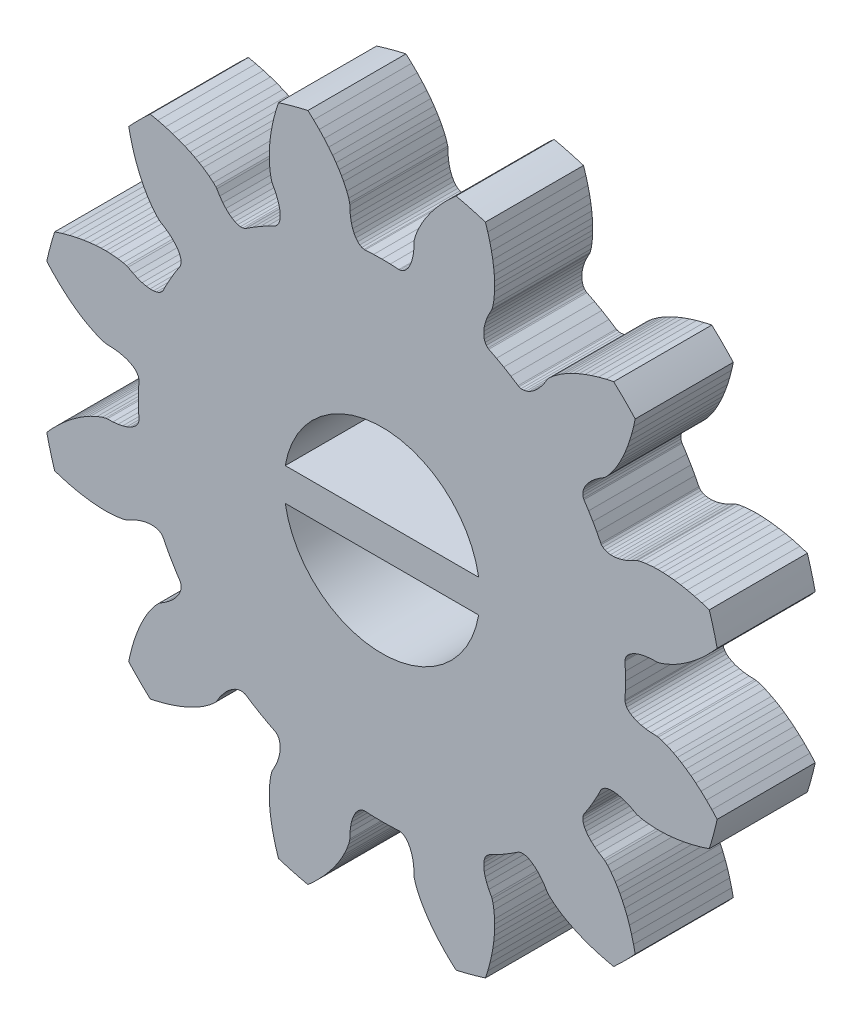
SolidWorks part; units mm, degrees
ref_plane "Płaszczyzna przednia" through (0, 0, 0) normal (0, 0, 1) x (1, 0, 0)
ref_plane "Płaszczyzna górna" through (0, 0, 0) normal (0, 1, 0) x (1, 0, 0)
ref_plane "Płaszczyzna prawa" through (0, 0, 0) normal (1, 0, 0) x (0, 0, -1)
sketch "szkic" plane through (0, 0, 0) normal (0, 0, 1) x (1, 0, 0)
  line L0 (13.3041, -6.8561) -> (13.3646, -6.6243)
  line L1 (13.3646, -6.6243) -> (13.4305, -6.4094)
  line L2 (13.4305, -6.4094) -> (13.5003, -6.2115)
  line L3 (13.5003, -6.2115) -> (13.5727, -6.0307)
  line L4 (13.5727, -6.0307) -> (13.6464, -5.8671)
  line L5 (13.6464, -5.8671) -> (13.7211, -5.718)
  line L6 (13.7211, -5.718) -> (13.7935, -5.5877)
  line L7 (13.7935, -5.5877) -> (13.8642, -5.472)
  line L8 (13.8642, -5.472) -> (13.9934, -5.2871)
  line L9 (13.9934, -5.2871) -> (14.1006, -5.158)
  line L10 (14.1006, -5.158) -> (14.1765, -5.0806)
  line L11 (14.1765, -5.0806) -> (14.2153, -5.0522)
  line L12 (14.2153, -5.0522) -> (14.3621, -4.9616)
  line L13 (14.3621, -4.9616) -> (14.4896, -4.8682)
  line L14 (14.4896, -4.8682) -> (14.5978, -4.7734)
  line L15 (14.5978, -4.7734) -> (14.6868, -4.6788)
  line L16 (14.6868, -4.6788) -> (14.7569, -4.5857)
  line L17 (14.7569, -4.5857) -> (14.8083, -4.4956)
  line L18 (14.8083, -4.4956) -> (14.8415, -4.4098)
  line L19 (14.8415, -4.4098) -> (14.8569, -4.3297)
  line L20 (14.8569, -4.3297) -> (14.8551, -4.2567)
  line L21 (14.8551, -4.2567) -> (14.8367, -4.192)
  line L22 (14.8367, -4.192) -> (14.8215, -4.1631)
  line L23 (14.8215, -4.1631) -> (14.6788, -3.9428)
  line L24 (14.6788, -3.9428) -> (14.5481, -3.725)
  line L25 (14.5481, -3.725) -> (14.4249, -3.5029)
  line L26 (14.4249, -3.5029) -> (14.3054, -3.2691)
  line L27 (14.3054, -3.2691) -> (14.288, -3.2416)
  line L28 (14.288, -3.2416) -> (14.2411, -3.1933)
  line L29 (14.2411, -3.1933) -> (14.1788, -3.1552)
  line L30 (14.1788, -3.1552) -> (14.1017, -3.1285)
  line L31 (14.1017, -3.1285) -> (14.0109, -3.1144)
  line L32 (14.0109, -3.1144) -> (13.9071, -3.1138)
  line L33 (13.9071, -3.1138) -> (13.7915, -3.128)
  line L34 (13.7915, -3.128) -> (13.665, -3.1577)
  line L35 (13.665, -3.1577) -> (13.5289, -3.2041)
  line L36 (13.5289, -3.2041) -> (13.3842, -3.2678)
  line L37 (13.3842, -3.2678) -> (13.2323, -3.3497)
  line L38 (13.2323, -3.3497) -> (13.1884, -3.369)
  line L39 (13.1884, -3.369) -> (13.0833, -3.3961)
  line L40 (13.0833, -3.3961) -> (12.918, -3.4244)
  line L41 (12.918, -3.4244) -> (12.6932, -3.4438)
  line L42 (12.6932, -3.4438) -> (12.5577, -3.4472)
  line L43 (12.5577, -3.4472) -> (12.4086, -3.4447)
  line L44 (12.4086, -3.4447) -> (12.2421, -3.4349)
  line L45 (12.2421, -3.4349) -> (12.0636, -3.4169)
  line L46 (12.0636, -3.4169) -> (11.8708, -3.3892)
  line L47 (11.8708, -3.3892) -> (11.6645, -3.3507)
  line L48 (11.6645, -3.3507) -> (11.4455, -3.3003)
  line L49 (11.4455, -3.3003) -> (11.2145, -3.2368)
  line L50 (11.2145, -3.2368) -> (10.9882, -3.1643)
  line L51 (10.7474, -2.2655) -> (10.9071, -2.0896)
  line L52 (10.9071, -2.0896) -> (11.0754, -1.9191)
  line L53 (11.0754, -1.9191) -> (11.2399, -1.7659)
  line L54 (11.2399, -1.7659) -> (11.3993, -1.6295)
  line L55 (11.3993, -1.6295) -> (11.5524, -1.5091)
  line L56 (11.5524, -1.5091) -> (11.698, -1.4042)
  line L57 (11.698, -1.4042) -> (11.8373, -1.3125)
  line L58 (11.8373, -1.3125) -> (11.9651, -1.2358)
  line L59 (11.9651, -1.2358) -> (12.0842, -1.171)
  line L60 (12.0842, -1.171) -> (12.2886, -1.0754)
  line L61 (12.2886, -1.0754) -> (12.4459, -1.0172)
  line L62 (12.4459, -1.0172) -> (12.5504, -0.9882)
  line L63 (12.5504, -0.9882) -> (12.5981, -0.983)
  line L64 (12.5981, -0.983) -> (12.7706, -0.9779)
  line L65 (12.7706, -0.9779) -> (12.9278, -0.9608)
  line L66 (12.9278, -0.9608) -> (13.0688, -0.9328)
  line L67 (13.0688, -0.9328) -> (13.1933, -0.8953)
  line L68 (13.1933, -0.8953) -> (13.3005, -0.8498)
  line L69 (13.3005, -0.8498) -> (13.3901, -0.7974)
  line L70 (13.3901, -0.7974) -> (13.4617, -0.7397)
  line L71 (13.4617, -0.7397) -> (13.515, -0.6781)
  line L72 (13.515, -0.6781) -> (13.55, -0.6139)
  line L73 (13.55, -0.6139) -> (13.5665, -0.5487)
  line L74 (13.5665, -0.5487) -> (13.5677, -0.5161)
  line L75 (13.5677, -0.5161) -> (13.5543, -0.2539)
  line L76 (13.5543, -0.2539) -> (13.55, 0)
  line L77 (13.55, 0) -> (13.5543, 0.2539)
  line L78 (13.5543, 0.2539) -> (13.5677, 0.5161)
  line L79 (13.5677, 0.5161) -> (13.5665, 0.5487)
  line L80 (13.5665, 0.5487) -> (13.55, 0.6139)
  line L81 (13.55, 0.6139) -> (13.515, 0.6781)
  line L82 (13.515, 0.6781) -> (13.4617, 0.7397)
  line L83 (13.4617, 0.7397) -> (13.3901, 0.7974)
  line L84 (13.3901, 0.7974) -> (13.3005, 0.8498)
  line L85 (13.3005, 0.8498) -> (13.1933, 0.8953)
  line L86 (13.1933, 0.8953) -> (13.0688, 0.9328)
  line L87 (13.0688, 0.9328) -> (12.9278, 0.9608)
  line L88 (12.9278, 0.9608) -> (12.7706, 0.9779)
  line L89 (12.7706, 0.9779) -> (12.5981, 0.983)
  line L90 (12.5981, 0.983) -> (12.5504, 0.9882)
  line L91 (12.5504, 0.9882) -> (12.4459, 1.0172)
  line L92 (12.4459, 1.0172) -> (12.2886, 1.0754)
  line L93 (12.2886, 1.0754) -> (12.0842, 1.171)
  line L94 (12.0842, 1.171) -> (11.9651, 1.2358)
  line L95 (11.9651, 1.2358) -> (11.8373, 1.3125)
  line L96 (11.8373, 1.3125) -> (11.698, 1.4042)
  line L97 (11.698, 1.4042) -> (11.5524, 1.5091)
  line L98 (11.5524, 1.5091) -> (11.3993, 1.6295)
  line L99 (11.3993, 1.6295) -> (11.2399, 1.7659)
  line L100 (11.2399, 1.7659) -> (11.0754, 1.9191)
  line L101 (11.0754, 1.9191) -> (10.9071, 2.0896)
  line L102 (10.9071, 2.0896) -> (10.7474, 2.2655)
  line L103 (10.9882, 3.1643) -> (11.2145, 3.2368)
  line L104 (11.2145, 3.2368) -> (11.4455, 3.3003)
  line L105 (11.4455, 3.3003) -> (11.6645, 3.3507)
  line L106 (11.6645, 3.3507) -> (11.8708, 3.3892)
  line L107 (11.8708, 3.3892) -> (12.0636, 3.4169)
  line L108 (12.0636, 3.4169) -> (12.2421, 3.4349)
  line L109 (12.2421, 3.4349) -> (12.4086, 3.4447)
  line L110 (12.4086, 3.4447) -> (12.5577, 3.4472)
  line L111 (12.5577, 3.4472) -> (12.6932, 3.4438)
  line L112 (12.6932, 3.4438) -> (12.918, 3.4244)
  line L113 (12.918, 3.4244) -> (13.0833, 3.3961)
  line L114 (13.0833, 3.3961) -> (13.1884, 3.369)
  line L115 (13.1884, 3.369) -> (13.2323, 3.3497)
  line L116 (13.2323, 3.3497) -> (13.3842, 3.2678)
  line L117 (13.3842, 3.2678) -> (13.5289, 3.2041)
  line L118 (13.5289, 3.2041) -> (13.665, 3.1577)
  line L119 (13.665, 3.1577) -> (13.7915, 3.128)
  line L120 (13.7915, 3.128) -> (13.9071, 3.1138)
  line L121 (13.9071, 3.1138) -> (14.0109, 3.1144)
  line L122 (14.0109, 3.1144) -> (14.1017, 3.1285)
  line L123 (14.1017, 3.1285) -> (14.1788, 3.1552)
  line L124 (14.1788, 3.1552) -> (14.2411, 3.1933)
  line L125 (14.2411, 3.1933) -> (14.288, 3.2416)
  line L126 (14.288, 3.2416) -> (14.3054, 3.2691)
  line L127 (14.3054, 3.2691) -> (14.4249, 3.5029)
  line L128 (14.4249, 3.5029) -> (14.5481, 3.725)
  line L129 (14.5481, 3.725) -> (14.6788, 3.9428)
  line L130 (14.6788, 3.9428) -> (14.8215, 4.1631)
  line L131 (14.8215, 4.1631) -> (14.8367, 4.192)
  line L132 (14.8367, 4.192) -> (14.8551, 4.2567)
  line L133 (14.8551, 4.2567) -> (14.8569, 4.3297)
  line L134 (14.8569, 4.3297) -> (14.8415, 4.4098)
  line L135 (14.8415, 4.4098) -> (14.8083, 4.4956)
  line L136 (14.8083, 4.4956) -> (14.7569, 4.5857)
  line L137 (14.7569, 4.5857) -> (14.6868, 4.6788)
  line L138 (14.6868, 4.6788) -> (14.5978, 4.7734)
  line L139 (14.5978, 4.7734) -> (14.4896, 4.8682)
  line L140 (14.4896, 4.8682) -> (14.3621, 4.9616)
  line L141 (14.3621, 4.9616) -> (14.2153, 5.0522)
  line L142 (14.2153, 5.0522) -> (14.1765, 5.0806)
  line L143 (14.1765, 5.0806) -> (14.1006, 5.158)
  line L144 (14.1006, 5.158) -> (13.9934, 5.2871)
  line L145 (13.9934, 5.2871) -> (13.8642, 5.472)
  line L146 (13.8642, 5.472) -> (13.7935, 5.5877)
  line L147 (13.7935, 5.5877) -> (13.7211, 5.718)
  line L148 (13.7211, 5.718) -> (13.6464, 5.8671)
  line L149 (13.6464, 5.8671) -> (13.5727, 6.0307)
  line L150 (13.5727, 6.0307) -> (13.5003, 6.2115)
  line L151 (13.5003, 6.2115) -> (13.4305, 6.4094)
  line L152 (13.4305, 6.4094) -> (13.3646, 6.6243)
  line L153 (13.3646, 6.6243) -> (13.3041, 6.8561)
  line L154 (13.3041, 6.8561) -> (13.2537, 7.0883)
  line L155 (13.9117, 7.7463) -> (14.1439, 7.6959)
  line L156 (14.1439, 7.6959) -> (14.3757, 7.6354)
  line L157 (14.3757, 7.6354) -> (14.5906, 7.5695)
  line L158 (14.5906, 7.5695) -> (14.7885, 7.4997)
  line L159 (14.7885, 7.4997) -> (14.9693, 7.4273)
  line L160 (14.9693, 7.4273) -> (15.1329, 7.3536)
  line L161 (15.1329, 7.3536) -> (15.282, 7.2789)
  line L162 (15.282, 7.2789) -> (15.4123, 7.2065)
  line L163 (15.4123, 7.2065) -> (15.528, 7.1358)
  line L164 (15.528, 7.1358) -> (15.7129, 7.0066)
  line L165 (15.7129, 7.0066) -> (15.842, 6.8994)
  line L166 (15.842, 6.8994) -> (15.9194, 6.8235)
  line L167 (15.9194, 6.8235) -> (15.9478, 6.7847)
  line L168 (15.9478, 6.7847) -> (16.0384, 6.6379)
  line L169 (16.0384, 6.6379) -> (16.1318, 6.5104)
  line L170 (16.1318, 6.5104) -> (16.2266, 6.4022)
  line L171 (16.2266, 6.4022) -> (16.3212, 6.3132)
  line L172 (16.3212, 6.3132) -> (16.4143, 6.2431)
  line L173 (16.4143, 6.2431) -> (16.5044, 6.1917)
  line L174 (16.5044, 6.1917) -> (16.5902, 6.1585)
  line L175 (16.5902, 6.1585) -> (16.6703, 6.1431)
  line L176 (16.6703, 6.1431) -> (16.7433, 6.1449)
  line L177 (16.7433, 6.1449) -> (16.808, 6.1633)
  line L178 (16.808, 6.1633) -> (16.8369, 6.1785)
  line L179 (16.8369, 6.1785) -> (17.0572, 6.3212)
  line L180 (17.0572, 6.3212) -> (17.275, 6.4519)
  line L181 (17.275, 6.4519) -> (17.4971, 6.5751)
  line L182 (17.4971, 6.5751) -> (17.7309, 6.6946)
  line L183 (17.7309, 6.6946) -> (17.7584, 6.712)
  line L184 (17.7584, 6.712) -> (17.8067, 6.7589)
  line L185 (17.8067, 6.7589) -> (17.8448, 6.8212)
  line L186 (17.8448, 6.8212) -> (17.8715, 6.8983)
  line L187 (17.8715, 6.8983) -> (17.8856, 6.9891)
  line L188 (17.8856, 6.9891) -> (17.8862, 7.0929)
  line L189 (17.8862, 7.0929) -> (17.872, 7.2085)
  line L190 (17.872, 7.2085) -> (17.8423, 7.335)
  line L191 (17.8423, 7.335) -> (17.7959, 7.4711)
  line L192 (17.7959, 7.4711) -> (17.7322, 7.6158)
  line L193 (17.7322, 7.6158) -> (17.6503, 7.7677)
  line L194 (17.6503, 7.7677) -> (17.631, 7.8116)
  line L195 (17.631, 7.8116) -> (17.6039, 7.9167)
  line L196 (17.6039, 7.9167) -> (17.5756, 8.082)
  line L197 (17.5756, 8.082) -> (17.5562, 8.3068)
  line L198 (17.5562, 8.3068) -> (17.5528, 8.4423)
  line L199 (17.5528, 8.4423) -> (17.5553, 8.5914)
  line L200 (17.5553, 8.5914) -> (17.5651, 8.7579)
  line L201 (17.5651, 8.7579) -> (17.5831, 8.9364)
  line L202 (17.5831, 8.9364) -> (17.6108, 9.1292)
  line L203 (17.6108, 9.1292) -> (17.6493, 9.3355)
  line L204 (17.6493, 9.3355) -> (17.6997, 9.5545)
  line L205 (17.6997, 9.5545) -> (17.7632, 9.7855)
  line L206 (17.7632, 9.7855) -> (17.8357, 10.0118)
  line L207 (18.7345, 10.2526) -> (18.9104, 10.0929)
  line L208 (18.9104, 10.0929) -> (19.0809, 9.9246)
  line L209 (19.0809, 9.9246) -> (19.2341, 9.7601)
  line L210 (19.2341, 9.7601) -> (19.3706, 9.6007)
  line L211 (19.3706, 9.6007) -> (19.4909, 9.4476)
  line L212 (19.4909, 9.4476) -> (19.5958, 9.302)
  line L213 (19.5958, 9.302) -> (19.6875, 9.1627)
  line L214 (19.6875, 9.1627) -> (19.7642, 9.0349)
  line L215 (19.7642, 9.0349) -> (19.829, 8.9158)
  line L216 (19.829, 8.9158) -> (19.9246, 8.7114)
  line L217 (19.9246, 8.7114) -> (19.9828, 8.5541)
  line L218 (19.9828, 8.5541) -> (20.0118, 8.4496)
  line L219 (20.0118, 8.4496) -> (20.017, 8.4019)
  line L220 (20.017, 8.4019) -> (20.0221, 8.2294)
  line L221 (20.0221, 8.2294) -> (20.0392, 8.0722)
  line L222 (20.0392, 8.0722) -> (20.0672, 7.9311)
  line L223 (20.0672, 7.9311) -> (20.1046, 7.8068)
  line L224 (20.1046, 7.8068) -> (20.1502, 7.6995)
  line L225 (20.1502, 7.6995) -> (20.2026, 7.61)
  line L226 (20.2026, 7.61) -> (20.2603, 7.5383)
  line L227 (20.2603, 7.5383) -> (20.3219, 7.485)
  line L228 (20.3219, 7.485) -> (20.3861, 7.45)
  line L229 (20.3861, 7.45) -> (20.4513, 7.4335)
  line L230 (20.4513, 7.4335) -> (20.4839, 7.4323)
  line L231 (20.4839, 7.4323) -> (20.7461, 7.4457)
  line L232 (20.7461, 7.4457) -> (21, 7.45)
  line L233 (21, 7.45) -> (21.2539, 7.4457)
  line L234 (21.2539, 7.4457) -> (21.5161, 7.4323)
  line L235 (21.5161, 7.4323) -> (21.5487, 7.4335)
  line L236 (21.5487, 7.4335) -> (21.6139, 7.45)
  line L237 (21.6139, 7.45) -> (21.6781, 7.485)
  line L238 (21.6781, 7.485) -> (21.7397, 7.5383)
  line L239 (21.7397, 7.5383) -> (21.7974, 7.61)
  line L240 (21.7974, 7.61) -> (21.8498, 7.6995)
  line L241 (21.8498, 7.6995) -> (21.8954, 7.8068)
  line L242 (21.8954, 7.8068) -> (21.9328, 7.9311)
  line L243 (21.9328, 7.9311) -> (21.9608, 8.0722)
  line L244 (21.9608, 8.0722) -> (21.9779, 8.2294)
  line L245 (21.9779, 8.2294) -> (21.983, 8.4019)
  line L246 (21.983, 8.4019) -> (21.9882, 8.4496)
  line L247 (21.9882, 8.4496) -> (22.0172, 8.5541)
  line L248 (22.0172, 8.5541) -> (22.0754, 8.7114)
  line L249 (22.0754, 8.7114) -> (22.171, 8.9158)
  line L250 (22.171, 8.9158) -> (22.2358, 9.0349)
  line L251 (22.2358, 9.0349) -> (22.3125, 9.1627)
  line L252 (22.3125, 9.1627) -> (22.4042, 9.302)
  line L253 (22.4042, 9.302) -> (22.5091, 9.4476)
  line L254 (22.5091, 9.4476) -> (22.6294, 9.6007)
  line L255 (22.6294, 9.6007) -> (22.7659, 9.7601)
  line L256 (22.7659, 9.7601) -> (22.9191, 9.9246)
  line L257 (22.9191, 9.9246) -> (23.0896, 10.0929)
  line L258 (23.0896, 10.0929) -> (23.2655, 10.2526)
  line L259 (24.1643, 10.0118) -> (24.2368, 9.7855)
  line L260 (24.2368, 9.7855) -> (24.3003, 9.5545)
  line L261 (24.3003, 9.5545) -> (24.3507, 9.3355)
  line L262 (24.3507, 9.3355) -> (24.3892, 9.1292)
  line L263 (24.3892, 9.1292) -> (24.4169, 8.9364)
  line L264 (24.4169, 8.9364) -> (24.4349, 8.7579)
  line L265 (24.4349, 8.7579) -> (24.4447, 8.5914)
  line L266 (24.4447, 8.5914) -> (24.4472, 8.4423)
  line L267 (24.4472, 8.4423) -> (24.4438, 8.3068)
  line L268 (24.4438, 8.3068) -> (24.4244, 8.082)
  line L269 (24.4244, 8.082) -> (24.3961, 7.9167)
  line L270 (24.3961, 7.9167) -> (24.369, 7.8116)
  line L271 (24.369, 7.8116) -> (24.3497, 7.7677)
  line L272 (24.3497, 7.7677) -> (24.2678, 7.6158)
  line L273 (24.2678, 7.6158) -> (24.2041, 7.4711)
  line L274 (24.2041, 7.4711) -> (24.1577, 7.335)
  line L275 (24.1577, 7.335) -> (24.128, 7.2085)
  line L276 (24.128, 7.2085) -> (24.1138, 7.0929)
  line L277 (24.1138, 7.0929) -> (24.1144, 6.9891)
  line L278 (24.1144, 6.9891) -> (24.1285, 6.8983)
  line L279 (24.1285, 6.8983) -> (24.1552, 6.8212)
  line L280 (24.1552, 6.8212) -> (24.1933, 6.7589)
  line L281 (24.1933, 6.7589) -> (24.2416, 6.712)
  line L282 (24.2416, 6.712) -> (24.2691, 6.6946)
  line L283 (24.2691, 6.6946) -> (24.5029, 6.5751)
  line L284 (24.5029, 6.5751) -> (24.725, 6.4519)
  line L285 (24.725, 6.4519) -> (24.9428, 6.3212)
  line L286 (24.9428, 6.3212) -> (25.1631, 6.1785)
  line L287 (25.1631, 6.1785) -> (25.192, 6.1633)
  line L288 (25.192, 6.1633) -> (25.2567, 6.1449)
  line L289 (25.2567, 6.1449) -> (25.3297, 6.1431)
  line L290 (25.3297, 6.1431) -> (25.4098, 6.1585)
  line L291 (25.4098, 6.1585) -> (25.4956, 6.1917)
  line L292 (25.4956, 6.1917) -> (25.5857, 6.2431)
  line L293 (25.5857, 6.2431) -> (25.6788, 6.3132)
  line L294 (25.6788, 6.3132) -> (25.7734, 6.4022)
  line L295 (25.7734, 6.4022) -> (25.8682, 6.5104)
  line L296 (25.8682, 6.5104) -> (25.9616, 6.6379)
  line L297 (25.9616, 6.6379) -> (26.0522, 6.7847)
  line L298 (26.0522, 6.7847) -> (26.0806, 6.8235)
  line L299 (26.0806, 6.8235) -> (26.158, 6.8994)
  line L300 (26.158, 6.8994) -> (26.2871, 7.0066)
  line L301 (26.2871, 7.0066) -> (26.472, 7.1358)
  line L302 (26.472, 7.1358) -> (26.5877, 7.2065)
  line L303 (26.5877, 7.2065) -> (26.718, 7.2789)
  line L304 (26.718, 7.2789) -> (26.8671, 7.3536)
  line L305 (26.8671, 7.3536) -> (27.0307, 7.4273)
  line L306 (27.0307, 7.4273) -> (27.2115, 7.4997)
  line L307 (27.2115, 7.4997) -> (27.4094, 7.5695)
  line L308 (27.4094, 7.5695) -> (27.6243, 7.6354)
  line L309 (27.6243, 7.6354) -> (27.8561, 7.6959)
  line L310 (27.8561, 7.6959) -> (28.0883, 7.7463)
  line L311 (28.7463, 7.0883) -> (28.6959, 6.8561)
  line L312 (28.6959, 6.8561) -> (28.6354, 6.6243)
  line L313 (28.6354, 6.6243) -> (28.5695, 6.4094)
  line L314 (28.5695, 6.4094) -> (28.4997, 6.2115)
  line L315 (28.4997, 6.2115) -> (28.4273, 6.0307)
  line L316 (28.4273, 6.0307) -> (28.3536, 5.8671)
  line L317 (28.3536, 5.8671) -> (28.2789, 5.718)
  line L318 (28.2789, 5.718) -> (28.2065, 5.5877)
  line L319 (28.2065, 5.5877) -> (28.1358, 5.472)
  line L320 (28.1358, 5.472) -> (28.0066, 5.2871)
  line L321 (28.0066, 5.2871) -> (27.8994, 5.158)
  line L322 (27.8994, 5.158) -> (27.8235, 5.0806)
  line L323 (27.8235, 5.0806) -> (27.7847, 5.0522)
  line L324 (27.7847, 5.0522) -> (27.6379, 4.9616)
  line L325 (27.6379, 4.9616) -> (27.5104, 4.8682)
  line L326 (27.5104, 4.8682) -> (27.4022, 4.7734)
  line L327 (27.4022, 4.7734) -> (27.3132, 4.6788)
  line L328 (27.3132, 4.6788) -> (27.2431, 4.5857)
  line L329 (27.2431, 4.5857) -> (27.1917, 4.4956)
  line L330 (27.1917, 4.4956) -> (27.1585, 4.4098)
  line L331 (27.1585, 4.4098) -> (27.1431, 4.3297)
  line L332 (27.1431, 4.3297) -> (27.1449, 4.2567)
  line L333 (27.1449, 4.2567) -> (27.1633, 4.192)
  line L334 (27.1633, 4.192) -> (27.1785, 4.1631)
  line L335 (27.1785, 4.1631) -> (27.3212, 3.9428)
  line L336 (27.3212, 3.9428) -> (27.4519, 3.725)
  line L337 (27.4519, 3.725) -> (27.5751, 3.5029)
  line L338 (27.5751, 3.5029) -> (27.6946, 3.2691)
  line L339 (27.6946, 3.2691) -> (27.712, 3.2416)
  line L340 (27.712, 3.2416) -> (27.7589, 3.1933)
  line L341 (27.7589, 3.1933) -> (27.8212, 3.1552)
  line L342 (27.8212, 3.1552) -> (27.8983, 3.1285)
  line L343 (27.8983, 3.1285) -> (27.9891, 3.1144)
  line L344 (27.9891, 3.1144) -> (28.0929, 3.1138)
  line L345 (28.0929, 3.1138) -> (28.2085, 3.128)
  line L346 (28.2085, 3.128) -> (28.335, 3.1577)
  line L347 (28.335, 3.1577) -> (28.4711, 3.2041)
  line L348 (28.4711, 3.2041) -> (28.6158, 3.2678)
  line L349 (28.6158, 3.2678) -> (28.7677, 3.3497)
  line L350 (28.7677, 3.3497) -> (28.8116, 3.369)
  line L351 (28.8116, 3.369) -> (28.9167, 3.3961)
  line L352 (28.9167, 3.3961) -> (29.082, 3.4244)
  line L353 (29.082, 3.4244) -> (29.3068, 3.4438)
  line L354 (29.3068, 3.4438) -> (29.4423, 3.4472)
  line L355 (29.4423, 3.4472) -> (29.5914, 3.4447)
  line L356 (29.5914, 3.4447) -> (29.7579, 3.4349)
  line L357 (29.7579, 3.4349) -> (29.9364, 3.4169)
  line L358 (29.9364, 3.4169) -> (30.1292, 3.3892)
  line L359 (30.1292, 3.3892) -> (30.3355, 3.3507)
  line L360 (30.3355, 3.3507) -> (30.5545, 3.3003)
  line L361 (30.5545, 3.3003) -> (30.7855, 3.2368)
  line L362 (30.7855, 3.2368) -> (31.0118, 3.1643)
  line L363 (31.2526, 2.2655) -> (31.0929, 2.0896)
  line L364 (31.0929, 2.0896) -> (30.9246, 1.9191)
  line L365 (30.9246, 1.9191) -> (30.7601, 1.7659)
  line L366 (30.7601, 1.7659) -> (30.6007, 1.6295)
  line L367 (30.6007, 1.6295) -> (30.4476, 1.5091)
  line L368 (30.4476, 1.5091) -> (30.302, 1.4042)
  line L369 (30.302, 1.4042) -> (30.1627, 1.3125)
  line L370 (30.1627, 1.3125) -> (30.0349, 1.2358)
  line L371 (30.0349, 1.2358) -> (29.9158, 1.171)
  line L372 (29.9158, 1.171) -> (29.7114, 1.0754)
  line L373 (29.7114, 1.0754) -> (29.5541, 1.0172)
  line L374 (29.5541, 1.0172) -> (29.4496, 0.9882)
  line L375 (29.4496, 0.9882) -> (29.4019, 0.983)
  line L376 (29.4019, 0.983) -> (29.2294, 0.9779)
  line L377 (29.2294, 0.9779) -> (29.0722, 0.9608)
  line L378 (29.0722, 0.9608) -> (28.9311, 0.9328)
  line L379 (28.9311, 0.9328) -> (28.8068, 0.8953)
  line L380 (28.8068, 0.8953) -> (28.6995, 0.8498)
  line L381 (28.6995, 0.8498) -> (28.61, 0.7974)
  line L382 (28.61, 0.7974) -> (28.5383, 0.7397)
  line L383 (28.5383, 0.7397) -> (28.485, 0.6781)
  line L384 (28.485, 0.6781) -> (28.45, 0.6139)
  line L385 (28.45, 0.6139) -> (28.4335, 0.5487)
  line L386 (28.4335, 0.5487) -> (28.4323, 0.5161)
  line L387 (28.4323, 0.5161) -> (28.4457, 0.2539)
  line L388 (28.4457, 0.2539) -> (28.45, 0)
  line L389 (28.45, 0) -> (28.4457, -0.2539)
  line L390 (28.4457, -0.2539) -> (28.4323, -0.5161)
  line L391 (28.4323, -0.5161) -> (28.4335, -0.5487)
  line L392 (28.4335, -0.5487) -> (28.45, -0.6139)
  line L393 (28.45, -0.6139) -> (28.485, -0.6781)
  line L394 (28.485, -0.6781) -> (28.5383, -0.7397)
  line L395 (28.5383, -0.7397) -> (28.61, -0.7974)
  line L396 (28.61, -0.7974) -> (28.6995, -0.8498)
  line L397 (28.6995, -0.8498) -> (28.8068, -0.8953)
  line L398 (28.8068, -0.8953) -> (28.9311, -0.9328)
  line L399 (28.9311, -0.9328) -> (29.0722, -0.9608)
  line L400 (29.0722, -0.9608) -> (29.2294, -0.9779)
  line L401 (29.2294, -0.9779) -> (29.4019, -0.983)
  line L402 (29.4019, -0.983) -> (29.4496, -0.9882)
  line L403 (29.4496, -0.9882) -> (29.5541, -1.0172)
  line L404 (29.5541, -1.0172) -> (29.7114, -1.0754)
  line L405 (29.7114, -1.0754) -> (29.9158, -1.171)
  line L406 (29.9158, -1.171) -> (30.0349, -1.2358)
  line L407 (30.0349, -1.2358) -> (30.1627, -1.3125)
  line L408 (30.1627, -1.3125) -> (30.302, -1.4042)
  line L409 (30.302, -1.4042) -> (30.4476, -1.5091)
  line L410 (30.4476, -1.5091) -> (30.6007, -1.6295)
  line L411 (30.6007, -1.6295) -> (30.7601, -1.7659)
  line L412 (30.7601, -1.7659) -> (30.9246, -1.9191)
  line L413 (30.9246, -1.9191) -> (31.0929, -2.0896)
  line L414 (31.0929, -2.0896) -> (31.2526, -2.2655)
  line L415 (31.0118, -3.1643) -> (30.7855, -3.2368)
  line L416 (30.7855, -3.2368) -> (30.5545, -3.3003)
  line L417 (30.5545, -3.3003) -> (30.3355, -3.3507)
  line L418 (30.3355, -3.3507) -> (30.1292, -3.3892)
  line L419 (30.1292, -3.3892) -> (29.9364, -3.4169)
  line L420 (29.9364, -3.4169) -> (29.7579, -3.4349)
  line L421 (29.7579, -3.4349) -> (29.5914, -3.4447)
  line L422 (29.5914, -3.4447) -> (29.4423, -3.4472)
  line L423 (29.4423, -3.4472) -> (29.3068, -3.4438)
  line L424 (29.3068, -3.4438) -> (29.082, -3.4244)
  line L425 (29.082, -3.4244) -> (28.9167, -3.3961)
  line L426 (28.9167, -3.3961) -> (28.8116, -3.369)
  line L427 (28.8116, -3.369) -> (28.7677, -3.3497)
  line L428 (28.7677, -3.3497) -> (28.6158, -3.2678)
  line L429 (28.6158, -3.2678) -> (28.4711, -3.2041)
  line L430 (28.4711, -3.2041) -> (28.335, -3.1577)
  line L431 (28.335, -3.1577) -> (28.2085, -3.128)
  line L432 (28.2085, -3.128) -> (28.0929, -3.1138)
  line L433 (28.0929, -3.1138) -> (27.9891, -3.1144)
  line L434 (27.9891, -3.1144) -> (27.8983, -3.1285)
  line L435 (27.8983, -3.1285) -> (27.8212, -3.1552)
  line L436 (27.8212, -3.1552) -> (27.7589, -3.1933)
  line L437 (27.7589, -3.1933) -> (27.712, -3.2416)
  line L438 (27.712, -3.2416) -> (27.6946, -3.2691)
  line L439 (27.6946, -3.2691) -> (27.5751, -3.5029)
  line L440 (27.5751, -3.5029) -> (27.4519, -3.725)
  line L441 (27.4519, -3.725) -> (27.3212, -3.9428)
  line L442 (27.3212, -3.9428) -> (27.1785, -4.1631)
  line L443 (27.1785, -4.1631) -> (27.1633, -4.192)
  line L444 (27.1633, -4.192) -> (27.1449, -4.2567)
  line L445 (27.1449, -4.2567) -> (27.1431, -4.3297)
  line L446 (27.1431, -4.3297) -> (27.1585, -4.4098)
  line L447 (27.1585, -4.4098) -> (27.1917, -4.4956)
  line L448 (27.1917, -4.4956) -> (27.2431, -4.5857)
  line L449 (27.2431, -4.5857) -> (27.3132, -4.6788)
  line L450 (27.3132, -4.6788) -> (27.4022, -4.7734)
  line L451 (27.4022, -4.7734) -> (27.5104, -4.8682)
  line L452 (27.5104, -4.8682) -> (27.6379, -4.9616)
  line L453 (27.6379, -4.9616) -> (27.7847, -5.0522)
  line L454 (27.7847, -5.0522) -> (27.8235, -5.0806)
  line L455 (27.8235, -5.0806) -> (27.8994, -5.158)
  line L456 (27.8994, -5.158) -> (28.0066, -5.2871)
  line L457 (28.0066, -5.2871) -> (28.1358, -5.472)
  line L458 (28.1358, -5.472) -> (28.2065, -5.5877)
  line L459 (28.2065, -5.5877) -> (28.2789, -5.718)
  line L460 (28.2789, -5.718) -> (28.3536, -5.8671)
  line L461 (28.3536, -5.8671) -> (28.4273, -6.0307)
  line L462 (28.4273, -6.0307) -> (28.4997, -6.2115)
  line L463 (28.4997, -6.2115) -> (28.5695, -6.4094)
  line L464 (28.5695, -6.4094) -> (28.6354, -6.6243)
  line L465 (28.6354, -6.6243) -> (28.6959, -6.8561)
  line L466 (28.6959, -6.8561) -> (28.7463, -7.0883)
  line L467 (28.0883, -7.7463) -> (27.8561, -7.6959)
  line L468 (27.8561, -7.6959) -> (27.6243, -7.6354)
  line L469 (27.6243, -7.6354) -> (27.4094, -7.5695)
  line L470 (27.4094, -7.5695) -> (27.2115, -7.4997)
  line L471 (27.2115, -7.4997) -> (27.0307, -7.4273)
  line L472 (27.0307, -7.4273) -> (26.8671, -7.3536)
  line L473 (26.8671, -7.3536) -> (26.718, -7.2789)
  line L474 (26.718, -7.2789) -> (26.5877, -7.2065)
  line L475 (26.5877, -7.2065) -> (26.472, -7.1358)
  line L476 (26.472, -7.1358) -> (26.2871, -7.0066)
  line L477 (26.2871, -7.0066) -> (26.158, -6.8994)
  line L478 (26.158, -6.8994) -> (26.0806, -6.8235)
  line L479 (26.0806, -6.8235) -> (26.0522, -6.7847)
  line L480 (26.0522, -6.7847) -> (25.9616, -6.6379)
  line L481 (25.9616, -6.6379) -> (25.8682, -6.5104)
  line L482 (25.8682, -6.5104) -> (25.7734, -6.4022)
  line L483 (25.7734, -6.4022) -> (25.6788, -6.3132)
  line L484 (25.6788, -6.3132) -> (25.5857, -6.2431)
  line L485 (25.5857, -6.2431) -> (25.4956, -6.1917)
  line L486 (25.4956, -6.1917) -> (25.4098, -6.1585)
  line L487 (25.4098, -6.1585) -> (25.3297, -6.1431)
  line L488 (25.3297, -6.1431) -> (25.2567, -6.1449)
  line L489 (25.2567, -6.1449) -> (25.192, -6.1633)
  line L490 (25.192, -6.1633) -> (25.1631, -6.1785)
  line L491 (25.1631, -6.1785) -> (24.9428, -6.3212)
  line L492 (24.9428, -6.3212) -> (24.725, -6.4519)
  line L493 (24.725, -6.4519) -> (24.5029, -6.5751)
  line L494 (24.5029, -6.5751) -> (24.2691, -6.6946)
  line L495 (24.2691, -6.6946) -> (24.2416, -6.712)
  line L496 (24.2416, -6.712) -> (24.1933, -6.7589)
  line L497 (24.1933, -6.7589) -> (24.1552, -6.8212)
  line L498 (24.1552, -6.8212) -> (24.1285, -6.8983)
  line L499 (24.1285, -6.8983) -> (24.1144, -6.9891)
  line L500 (24.1144, -6.9891) -> (24.1138, -7.0929)
  line L501 (24.1138, -7.0929) -> (24.128, -7.2085)
  line L502 (24.128, -7.2085) -> (24.1577, -7.335)
  line L503 (24.1577, -7.335) -> (24.2041, -7.4711)
  line L504 (24.2041, -7.4711) -> (24.2678, -7.6158)
  line L505 (24.2678, -7.6158) -> (24.3497, -7.7677)
  line L506 (24.3497, -7.7677) -> (24.369, -7.8116)
  line L507 (24.369, -7.8116) -> (24.3961, -7.9167)
  line L508 (24.3961, -7.9167) -> (24.4244, -8.082)
  line L509 (24.4244, -8.082) -> (24.4438, -8.3068)
  line L510 (24.4438, -8.3068) -> (24.4472, -8.4423)
  line L511 (24.4472, -8.4423) -> (24.4447, -8.5914)
  line L512 (24.4447, -8.5914) -> (24.4349, -8.7579)
  line L513 (24.4349, -8.7579) -> (24.4169, -8.9364)
  line L514 (24.4169, -8.9364) -> (24.3892, -9.1292)
  line L515 (24.3892, -9.1292) -> (24.3507, -9.3355)
  line L516 (24.3507, -9.3355) -> (24.3003, -9.5545)
  line L517 (24.3003, -9.5545) -> (24.2368, -9.7855)
  line L518 (24.2368, -9.7855) -> (24.1643, -10.0118)
  line L519 (23.2655, -10.2526) -> (23.0896, -10.0929)
  line L520 (23.0896, -10.0929) -> (22.9191, -9.9246)
  line L521 (22.9191, -9.9246) -> (22.7659, -9.7601)
  line L522 (22.7659, -9.7601) -> (22.6294, -9.6007)
  line L523 (22.6294, -9.6007) -> (22.5091, -9.4476)
  line L524 (22.5091, -9.4476) -> (22.4042, -9.302)
  line L525 (22.4042, -9.302) -> (22.3125, -9.1627)
  line L526 (22.3125, -9.1627) -> (22.2358, -9.0349)
  line L527 (22.2358, -9.0349) -> (22.171, -8.9158)
  line L528 (22.171, -8.9158) -> (22.0754, -8.7114)
  line L529 (22.0754, -8.7114) -> (22.0172, -8.5541)
  line L530 (22.0172, -8.5541) -> (21.9882, -8.4496)
  line L531 (21.9882, -8.4496) -> (21.983, -8.4019)
  line L532 (21.983, -8.4019) -> (21.9779, -8.2294)
  line L533 (21.9779, -8.2294) -> (21.9608, -8.0722)
  line L534 (21.9608, -8.0722) -> (21.9328, -7.9311)
  line L535 (21.9328, -7.9311) -> (21.8954, -7.8068)
  line L536 (21.8954, -7.8068) -> (21.8498, -7.6995)
  line L537 (21.8498, -7.6995) -> (21.7974, -7.61)
  line L538 (21.7974, -7.61) -> (21.7397, -7.5383)
  line L539 (21.7397, -7.5383) -> (21.6781, -7.485)
  line L540 (21.6781, -7.485) -> (21.6139, -7.45)
  line L541 (21.6139, -7.45) -> (21.5487, -7.4335)
  line L542 (21.5487, -7.4335) -> (21.5161, -7.4323)
  line L543 (21.5161, -7.4323) -> (21.2539, -7.4457)
  line L544 (21.2539, -7.4457) -> (21, -7.45)
  line L545 (21, -7.45) -> (20.7461, -7.4457)
  line L546 (20.7461, -7.4457) -> (20.4839, -7.4323)
  line L547 (20.4839, -7.4323) -> (20.4513, -7.4335)
  line L548 (20.4513, -7.4335) -> (20.3861, -7.45)
  line L549 (20.3861, -7.45) -> (20.3219, -7.485)
  line L550 (20.3219, -7.485) -> (20.2603, -7.5383)
  line L551 (20.2603, -7.5383) -> (20.2026, -7.61)
  line L552 (20.2026, -7.61) -> (20.1502, -7.6995)
  line L553 (20.1502, -7.6995) -> (20.1046, -7.8068)
  line L554 (20.1046, -7.8068) -> (20.0672, -7.9311)
  line L555 (20.0672, -7.9311) -> (20.0392, -8.0722)
  line L556 (20.0392, -8.0722) -> (20.0221, -8.2294)
  line L557 (20.0221, -8.2294) -> (20.017, -8.4019)
  line L558 (20.017, -8.4019) -> (20.0118, -8.4496)
  line L559 (20.0118, -8.4496) -> (19.9828, -8.5541)
  line L560 (19.9828, -8.5541) -> (19.9246, -8.7114)
  line L561 (19.9246, -8.7114) -> (19.829, -8.9158)
  line L562 (19.829, -8.9158) -> (19.7642, -9.0349)
  line L563 (19.7642, -9.0349) -> (19.6875, -9.1627)
  line L564 (19.6875, -9.1627) -> (19.5958, -9.302)
  line L565 (19.5958, -9.302) -> (19.4909, -9.4476)
  line L566 (19.4909, -9.4476) -> (19.3706, -9.6007)
  line L567 (19.3706, -9.6007) -> (19.2341, -9.7601)
  line L568 (19.2341, -9.7601) -> (19.0809, -9.9246)
  line L569 (19.0809, -9.9246) -> (18.9104, -10.0929)
  line L570 (18.9104, -10.0929) -> (18.7345, -10.2526)
  line L571 (17.8357, -10.0118) -> (17.7632, -9.7855)
  line L572 (17.7632, -9.7855) -> (17.6997, -9.5545)
  line L573 (17.6997, -9.5545) -> (17.6493, -9.3355)
  line L574 (17.6493, -9.3355) -> (17.6108, -9.1292)
  line L575 (17.6108, -9.1292) -> (17.5831, -8.9364)
  line L576 (17.5831, -8.9364) -> (17.5651, -8.7579)
  line L577 (17.5651, -8.7579) -> (17.5553, -8.5914)
  line L578 (17.5553, -8.5914) -> (17.5528, -8.4423)
  line L579 (17.5528, -8.4423) -> (17.5562, -8.3068)
  line L580 (17.5562, -8.3068) -> (17.5756, -8.082)
  line L581 (17.5756, -8.082) -> (17.6039, -7.9167)
  line L582 (17.6039, -7.9167) -> (17.631, -7.8116)
  line L583 (17.631, -7.8116) -> (17.6503, -7.7677)
  line L584 (17.6503, -7.7677) -> (17.7322, -7.6158)
  line L585 (17.7322, -7.6158) -> (17.7959, -7.4711)
  line L586 (17.7959, -7.4711) -> (17.8423, -7.335)
  line L587 (17.8423, -7.335) -> (17.872, -7.2085)
  line L588 (17.872, -7.2085) -> (17.8862, -7.0929)
  line L589 (17.8862, -7.0929) -> (17.8856, -6.9891)
  line L590 (17.8856, -6.9891) -> (17.8715, -6.8983)
  line L591 (17.8715, -6.8983) -> (17.8448, -6.8212)
  line L592 (17.8448, -6.8212) -> (17.8067, -6.7589)
  line L593 (17.8067, -6.7589) -> (17.7584, -6.712)
  line L594 (17.7584, -6.712) -> (17.7309, -6.6946)
  line L595 (17.7309, -6.6946) -> (17.4971, -6.5751)
  line L596 (17.4971, -6.5751) -> (17.275, -6.4519)
  line L597 (17.275, -6.4519) -> (17.0572, -6.3212)
  line L598 (17.0572, -6.3212) -> (16.8369, -6.1785)
  line L599 (16.8369, -6.1785) -> (16.808, -6.1633)
  line L600 (16.808, -6.1633) -> (16.7433, -6.1449)
  line L601 (16.7433, -6.1449) -> (16.6703, -6.1431)
  line L602 (16.6703, -6.1431) -> (16.5902, -6.1585)
  line L603 (16.5902, -6.1585) -> (16.5044, -6.1917)
  line L604 (16.5044, -6.1917) -> (16.4143, -6.2431)
  line L605 (16.4143, -6.2431) -> (16.3212, -6.3132)
  line L606 (16.3212, -6.3132) -> (16.2266, -6.4022)
  line L607 (16.2266, -6.4022) -> (16.1318, -6.5104)
  line L608 (16.1318, -6.5104) -> (16.0384, -6.6379)
  line L609 (16.0384, -6.6379) -> (15.9478, -6.7847)
  line L610 (15.9478, -6.7847) -> (15.9194, -6.8235)
  line L611 (15.9194, -6.8235) -> (15.842, -6.8994)
  line L612 (15.842, -6.8994) -> (15.7129, -7.0066)
  line L613 (15.7129, -7.0066) -> (15.528, -7.1358)
  line L614 (15.528, -7.1358) -> (15.4123, -7.2065)
  line L615 (15.4123, -7.2065) -> (15.282, -7.2789)
  line L616 (15.282, -7.2789) -> (15.1329, -7.3536)
  line L617 (15.1329, -7.3536) -> (14.9693, -7.4273)
  line L618 (14.9693, -7.4273) -> (14.7885, -7.4997)
  line L619 (14.7885, -7.4997) -> (14.5906, -7.5695)
  line L620 (14.5906, -7.5695) -> (14.3757, -7.6354)
  line L621 (14.3757, -7.6354) -> (14.1439, -7.6959)
  line L622 (14.1439, -7.6959) -> (13.9117, -7.7463)
  line L623 (13.2537, -7.0883) -> (13.3041, -6.8561)
  line L627 (20.2026, 0.5) -> (23.958, 0.5) construction
  line L628 (23.958, 0.5) -> (18.042, 0.5) construction
  line L629 (20.2026, -0.5) -> (23.958, -0.5) construction
  line L630 (23.958, -0.5) -> (18.042, -0.5) construction
  line L631 (18.042, 0.5) -> (23.958, 0.5)
  line L632 (18.042, -0.5) -> (23.958, -0.5)
  arc A0 (18.042, -0.5) -> (23.958, -0.5) centre (21, 0) ccw
  arc A1 (23.958, 0.5) -> (18.042, 0.5) centre (21, 0) ccw
  arc A2 (10.7474, -2.2655) -> (10.9882, -3.1643) centre (21, 0) ccw
  arc A3 (10.9882, 3.1643) -> (10.7474, 2.2655) centre (21, 0) ccw
  arc A4 (13.9117, 7.7463) -> (13.2537, 7.0883) centre (21, 0) ccw
  arc A5 (18.7345, 10.2526) -> (17.8357, 10.0118) centre (21, 0) ccw
  arc A6 (24.1643, 10.0118) -> (23.2655, 10.2526) centre (21, 0) ccw
  arc A7 (28.7463, 7.0883) -> (28.0883, 7.7463) centre (21, 0) ccw
  arc A8 (31.2526, 2.2655) -> (31.0118, 3.1643) centre (21, 0) ccw
  arc A9 (31.0118, -3.1643) -> (31.2526, -2.2655) centre (21, 0) ccw
  arc A10 (28.0883, -7.7463) -> (28.7463, -7.0883) centre (21, 0) ccw
  arc A11 (23.2655, -10.2526) -> (24.1643, -10.0118) centre (21, 0) ccw
  arc A12 (17.8357, -10.0118) -> (18.7345, -10.2526) centre (21, 0) ccw
  arc A13 (13.2537, -7.0883) -> (13.9117, -7.7463) centre (21, 0) ccw
  dimension "D1" = 6
extrude "Dodanie-wyciągnięcie1" add sketch "szkic" along normal blind 3
